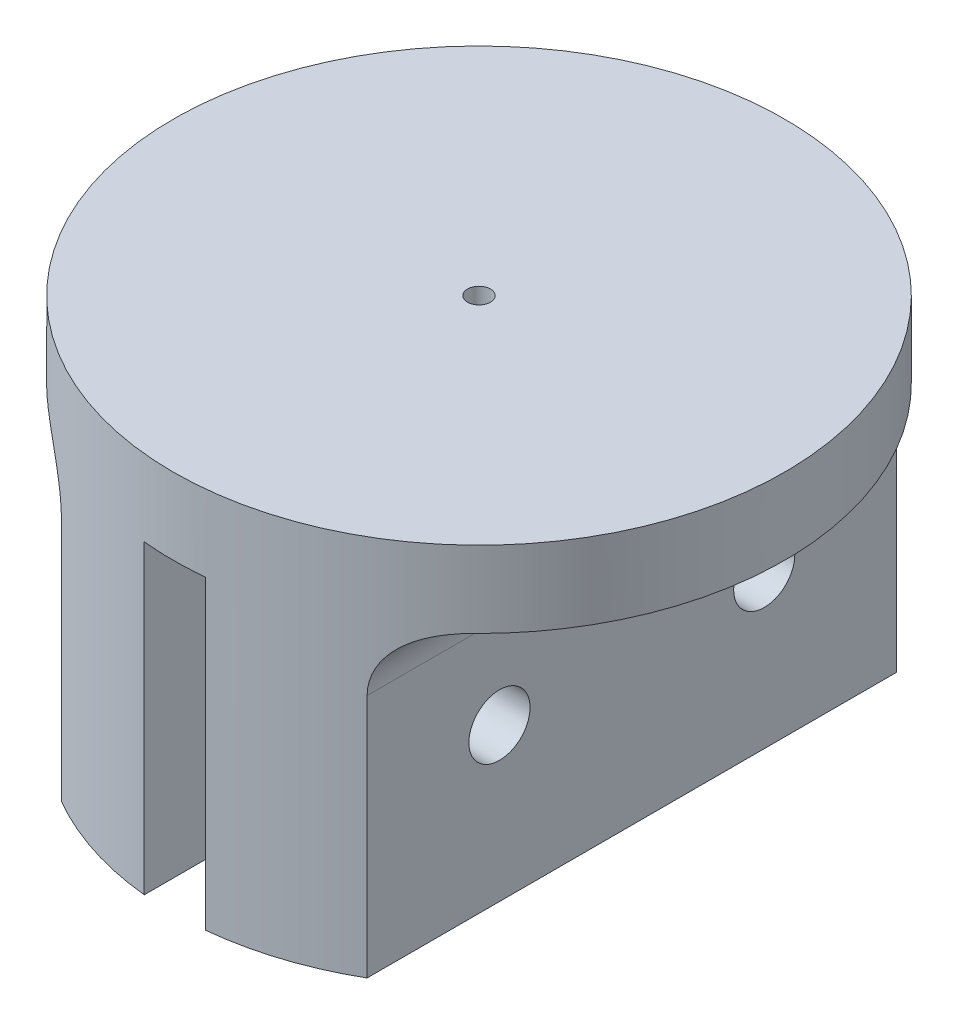
SolidWorks part; units mm, degrees
ref_plane "Plano frontal" through (0, 0, 0) normal (0, 0, 1) x (1, 0, 0)
ref_plane "Plano superior" through (0, 0, 0) normal (0, 1, 0) x (1, 0, 0)
ref_plane "Plano direito" through (0, 0, 0) normal (1, 0, 0) x (0, 0, -1)
sketch "Esboço1" plane through (0, 0, 0) normal (0, 1, 0) x (1, 0, 0)
  circle A0 centre (0, 0) radius 20
  circle A1 centre (0, 0) radius 0.75
  dimension "D1" = 40
  dimension "D2" = 1.5
extrude "Ressalto-extrusão1" add sketch "Esboço1" along normal blind 25
sketch "Esboço2" plane through (0, 0, 0) normal (0, 1, 0) x (1, 0, 0)
  line L0 (0, 20) -> (0, -20) construction
  line L2 (-2, 20.7716) -> (2, 20.7716)
  line L3 (-2, 20.7716) -> (-2, -21.2997)
  line L4 (-2, -21.2997) -> (2, -21.2997)
  line L5 (2, 20.7716) -> (2, -21.2997)
  line L6 (-25.1386, 20) -> (-10, 20)
  line L7 (-25.1386, 20) -> (-25.1386, -20)
  line L8 (-25.1386, -20) -> (-10, -20)
  line L9 (-10, 20) -> (-10, -20)
  line L10 (22.2635, 20.7716) -> (10, 20.7716)
  line L11 (22.2635, 20.7716) -> (22.2635, -21.2997)
  line L12 (22.2635, -21.2997) -> (10, -21.2997)
  line L13 (10, 20.7716) -> (10, -21.2997)
  circle A0 centre (0, 0) radius 20 construction
  dimension "D1" = 2
  dimension "D2" = 2
  dimension "D3" = 10
  dimension "D4" = 10
extrude "Corte-extrusão1" cut sketch "Esboço2" along normal blind 20
sketch "Esboço3" plane through (0, 0, 0) normal (1, 0, 0) x (0, 0, -1)
  line L0 (-17.3205, 10) -> (17.3205, 10) construction
  line L1 (-17.3205, 20) -> (-17.3205, 0) construction
  line L2 (17.3205, 0) -> (17.3205, 20) construction
  line L3 (17.3205, 10) -> (17.3205, 20) construction
  line L4 (17.3205, 20) -> (0, 20) construction
  line L5 (-17.3205, 20) -> (17.3205, 20) construction
  line L6 (0, 20) -> (0, 0) construction
  line L7 (8.6603, 20) -> (8.6603, 0) construction
  line L8 (-17.3205, 0) -> (17.3205, 0) construction
  line L9 (8.6603, 0) -> (-17.3205, 0) construction
  line L10 (-17.3205, 0) -> (-17.3205, 20) construction
  line L11 (-17.3205, 20) -> (0, 20) construction
  line L12 (0, 20) -> (-17.3205, 0) construction
  line L13 (-8.6603, 20) -> (-8.6603, 0) construction
  circle A0 centre (-8.6603, 10) radius 2
  circle A1 centre (8.6603, 10) radius 2
  dimension "D1" = 4
  dimension "D2" = 4
extrude "Corte-extrusão2" cut sketch "Esboço3" against normal blind 20 and the other way blind 20
fillet "Filete1" radius 4 2 edges at (-10, 20, 0) (10, 20, 0)
